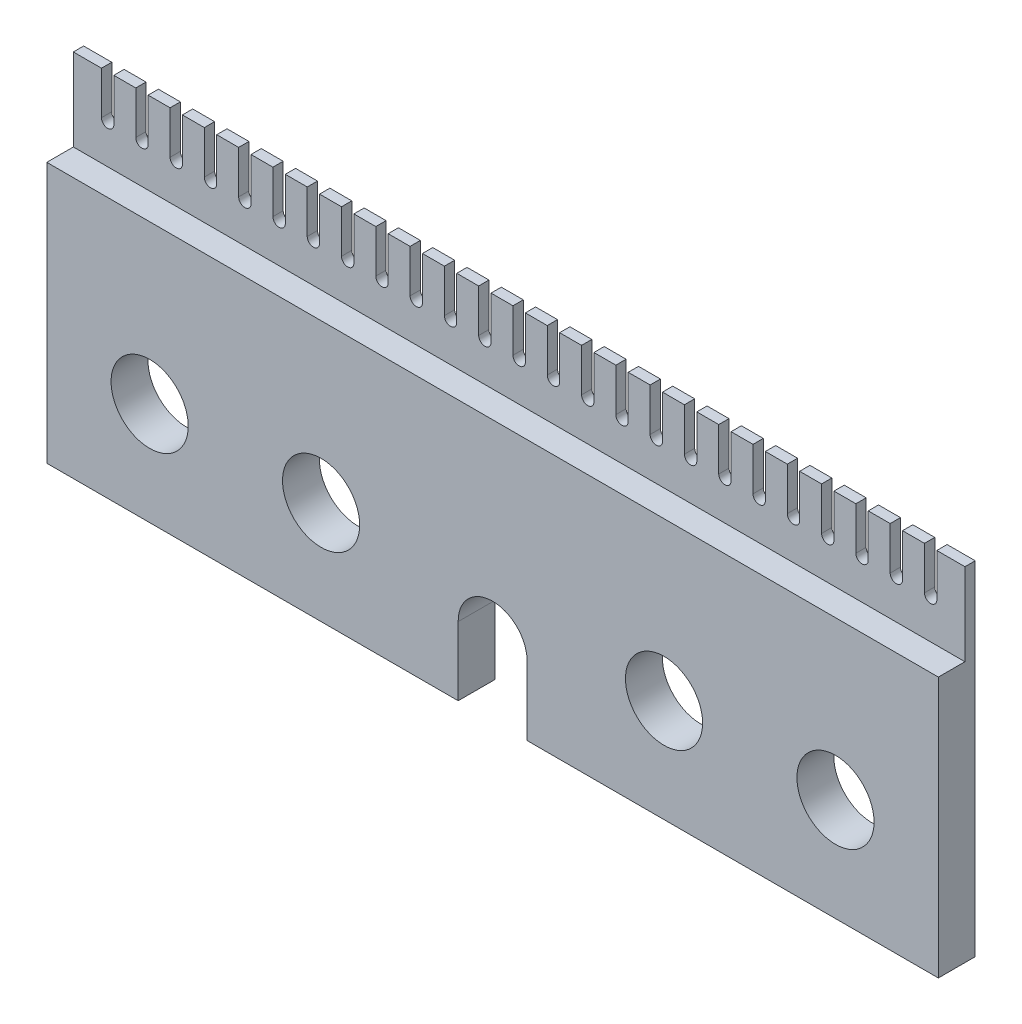
SolidWorks part; units mm, degrees
ref_plane "Front Plane" through (0, 0, 0) normal (0, 0, 1) x (1, 0, 0)
ref_plane "Top Plane" through (0, 0, 0) normal (0, 1, 0) x (1, 0, 0)
ref_plane "Right Plane" through (0, 0, 0) normal (1, 0, 0) x (0, 0, -1)
sketch "Sketch1" plane through (0, 0, 0) normal (0, 0, 1) x (1, 0, 0)
  line L0 (2.3988, -11.3273) -> (26.3844, -11.3273)
  line L1 (-25.6156, 8.6727) -> (-23.9756, 8.6727)
  line L2 (-25.6156, 8.6727) -> (-25.6156, -11.3273)
  line L3 (-25.6156, -11.3273) -> (-1.6212, -11.3273)
  line L4 (26.3844, 8.6727) -> (26.3844, -11.3273)
  line L5 (-23.2556, 8.6727) -> (-21.9756, 8.6727)
  line L6 (-1.6212, -11.3273) -> (-1.6212, -7.3273)
  line L7 (-21.2556, 8.6727) -> (-19.9756, 8.6727)
  line L8 (2.3988, -11.3273) -> (2.3988, -7.2968)
  line L9 (-21.2556, 8.6727) -> (-21.2556, 6.1727)
  line L10 (-23.9756, 8.6727) -> (-23.9756, 6.1727)
  line L11 (-21.9756, 8.6727) -> (-21.9756, 6.1727)
  line L12 (-23.2556, 8.6727) -> (-23.2556, 6.1727)
  line L13 (-19.2556, 8.6727) -> (-17.9756, 8.6727)
  line L14 (-19.2556, 8.6727) -> (-19.2556, 6.1727)
  line L15 (-19.9756, 8.6727) -> (-19.9756, 6.1727)
  line L16 (-17.2556, 8.6727) -> (-15.9756, 8.6727)
  line L17 (-17.2556, 8.6727) -> (-17.2556, 6.1727)
  line L18 (-17.9756, 8.6727) -> (-17.9756, 6.1727)
  line L19 (-15.2556, 8.6727) -> (-13.9756, 8.6727)
  line L20 (-15.2556, 8.6727) -> (-15.2556, 6.1727)
  line L21 (-15.9756, 8.6727) -> (-15.9756, 6.1727)
  line L22 (-13.2556, 8.6727) -> (-11.9756, 8.6727)
  line L23 (-13.2556, 8.6727) -> (-13.2556, 6.1727)
  line L24 (-13.9756, 8.6727) -> (-13.9756, 6.1727)
  line L25 (-11.2556, 8.6727) -> (-9.9756, 8.6727)
  line L26 (-11.2556, 8.6727) -> (-11.2556, 6.1727)
  line L27 (-11.9756, 8.6727) -> (-11.9756, 6.1727)
  line L28 (-9.2556, 8.6727) -> (-7.9756, 8.6727)
  line L29 (-9.2556, 8.6727) -> (-9.2556, 6.1727)
  line L30 (-9.9756, 8.6727) -> (-9.9756, 6.1727)
  line L31 (-7.2556, 8.6727) -> (-5.9756, 8.6727)
  line L32 (-7.2556, 8.6727) -> (-7.2556, 6.1727)
  line L33 (-7.9756, 8.6727) -> (-7.9756, 6.1727)
  line L34 (-5.2556, 8.6727) -> (-3.9756, 8.6727)
  line L35 (-5.2556, 8.6727) -> (-5.2556, 6.1727)
  line L36 (-5.9756, 8.6727) -> (-5.9756, 6.1727)
  line L37 (-3.2556, 8.6727) -> (-1.9756, 8.6727)
  line L38 (-3.2556, 8.6727) -> (-3.2556, 6.1727)
  line L39 (-3.9756, 8.6727) -> (-3.9756, 6.1727)
  line L40 (-1.2556, 8.6727) -> (0.0244, 8.6727)
  line L41 (-1.2556, 8.6727) -> (-1.2556, 6.1727)
  line L42 (-1.9756, 8.6727) -> (-1.9756, 6.1727)
  line L43 (0.7444, 8.6727) -> (2.0244, 8.6727)
  line L44 (0.7444, 8.6727) -> (0.7444, 6.1727)
  line L45 (0.0244, 8.6727) -> (0.0244, 6.1727)
  line L46 (2.7444, 8.6727) -> (4.0244, 8.6727)
  line L47 (2.7444, 8.6727) -> (2.7444, 6.1727)
  line L48 (2.0244, 8.6727) -> (2.0244, 6.1727)
  line L49 (4.7444, 8.6727) -> (6.0244, 8.6727)
  line L50 (4.7444, 8.6727) -> (4.7444, 6.1727)
  line L51 (4.0244, 8.6727) -> (4.0244, 6.1727)
  line L52 (6.7444, 8.6727) -> (8.0244, 8.6727)
  line L53 (6.7444, 8.6727) -> (6.7444, 6.1727)
  line L54 (6.0244, 8.6727) -> (6.0244, 6.1727)
  line L55 (8.7444, 8.6727) -> (10.0244, 8.6727)
  line L56 (8.7444, 8.6727) -> (8.7444, 6.1727)
  line L57 (8.0244, 8.6727) -> (8.0244, 6.1727)
  line L58 (10.7444, 8.6727) -> (12.0244, 8.6727)
  line L59 (10.7444, 8.6727) -> (10.7444, 6.1727)
  line L60 (10.0244, 8.6727) -> (10.0244, 6.1727)
  line L61 (12.7444, 8.6727) -> (14.0244, 8.6727)
  line L62 (12.7444, 8.6727) -> (12.7444, 6.1727)
  line L63 (12.0244, 8.6727) -> (12.0244, 6.1727)
  line L64 (14.7444, 8.6727) -> (16.0244, 8.6727)
  line L65 (14.7444, 8.6727) -> (14.7444, 6.1727)
  line L66 (14.0244, 8.6727) -> (14.0244, 6.1727)
  line L67 (16.7444, 8.6727) -> (18.0244, 8.6727)
  line L68 (16.7444, 8.6727) -> (16.7444, 6.1727)
  line L69 (16.0244, 8.6727) -> (16.0244, 6.1727)
  line L70 (18.7444, 8.6727) -> (20.0244, 8.6727)
  line L71 (18.7444, 8.6727) -> (18.7444, 6.1727)
  line L72 (18.0244, 8.6727) -> (18.0244, 6.1727)
  line L73 (20.7444, 8.6727) -> (22.0244, 8.6727)
  line L74 (20.7444, 8.6727) -> (20.7444, 6.1727)
  line L75 (20.0244, 8.6727) -> (20.0244, 6.1727)
  line L76 (22.7444, 8.6727) -> (24.0244, 8.6727)
  line L77 (22.7444, 8.6727) -> (22.7444, 6.1727)
  line L78 (22.0244, 8.6727) -> (22.0244, 6.1727)
  line L79 (24.7444, 8.6727) -> (26.0244, 8.6727)
  line L80 (24.7444, 8.6727) -> (24.7444, 6.1727)
  line L81 (24.0244, 8.6727) -> (24.0244, 6.1727)
  line L82 (26.0244, 8.6727) -> (26.3844, 8.6727)
  arc A0 (-23.9756, 6.1727) -> (-23.2556, 6.1727) centre (-23.6156, 6.1727) ccw
  arc A1 (2.3988, -7.2968) -> (-1.6212, -7.3273) centre (0.3887, -7.3038) ccw
  circle A2 centre (-19.6156, -5.3273) radius 2.25
  circle A3 centre (-9.6156, -5.3273) radius 2.25
  circle A4 centre (10.3844, -5.3273) radius 2.25
  circle A5 centre (20.3844, -5.3273) radius 2.25
  arc A6 (-21.9756, 6.1727) -> (-21.2556, 6.1727) centre (-21.6156, 6.1727) ccw
  arc A7 (-19.9756, 6.1727) -> (-19.2556, 6.1727) centre (-19.6156, 6.1727) ccw
  arc A8 (-17.9756, 6.1727) -> (-17.2556, 6.1727) centre (-17.6156, 6.1727) ccw
  arc A9 (-15.9756, 6.1727) -> (-15.2556, 6.1727) centre (-15.6156, 6.1727) ccw
  arc A10 (-13.9756, 6.1727) -> (-13.2556, 6.1727) centre (-13.6156, 6.1727) ccw
  arc A11 (-11.9756, 6.1727) -> (-11.2556, 6.1727) centre (-11.6156, 6.1727) ccw
  arc A12 (-9.9756, 6.1727) -> (-9.2556, 6.1727) centre (-9.6156, 6.1727) ccw
  arc A13 (-7.9756, 6.1727) -> (-7.2556, 6.1727) centre (-7.6156, 6.1727) ccw
  arc A14 (-5.9756, 6.1727) -> (-5.2556, 6.1727) centre (-5.6156, 6.1727) ccw
  arc A15 (-3.9756, 6.1727) -> (-3.2556, 6.1727) centre (-3.6156, 6.1727) ccw
  arc A16 (-1.9756, 6.1727) -> (-1.2556, 6.1727) centre (-1.6156, 6.1727) ccw
  arc A17 (0.0244, 6.1727) -> (0.7444, 6.1727) centre (0.3844, 6.1727) ccw
  arc A18 (2.0244, 6.1727) -> (2.7444, 6.1727) centre (2.3844, 6.1727) ccw
  arc A19 (4.0244, 6.1727) -> (4.7444, 6.1727) centre (4.3844, 6.1727) ccw
  arc A20 (6.0244, 6.1727) -> (6.7444, 6.1727) centre (6.3844, 6.1727) ccw
  arc A21 (8.0244, 6.1727) -> (8.7444, 6.1727) centre (8.3844, 6.1727) ccw
  arc A22 (10.0244, 6.1727) -> (10.7444, 6.1727) centre (10.3844, 6.1727) ccw
  arc A23 (12.0244, 6.1727) -> (12.7444, 6.1727) centre (12.3844, 6.1727) ccw
  arc A24 (14.0244, 6.1727) -> (14.7444, 6.1727) centre (14.3844, 6.1727) ccw
  arc A25 (16.0244, 6.1727) -> (16.7444, 6.1727) centre (16.3844, 6.1727) ccw
  arc A26 (18.0244, 6.1727) -> (18.7444, 6.1727) centre (18.3844, 6.1727) ccw
  arc A27 (20.0244, 6.1727) -> (20.7444, 6.1727) centre (20.3844, 6.1727) ccw
  arc A28 (22.0244, 6.1727) -> (22.7444, 6.1727) centre (22.3844, 6.1727) ccw
  arc A29 (24.0244, 6.1727) -> (24.7444, 6.1727) centre (24.3844, 6.1727) ccw
  dimension "D3" = 4.5
  dimension "D1" = 52
  dimension "D2" = 20
  dimension "D4" = 6
  dimension "D5" = 6
  dimension "D6" = 16
  dimension "D7" = 36
  dimension "D8" = 46
  dimension "D10" = 4
  dimension "D11" = 4.02
  dimension "D12" = 2
  dimension "D13" = 0.36
  dimension "D14" = 17.5
  dimension "D15" = 1.28
  dimension "D17" = 20
  dimension "D16" = 25
extrude "Boss-Extrude1" add sketch "Sketch1" along normal blind 2.15
sketch "Sketch2" plane through (-25.6156, 0, 0) normal (-1, 0, 0) x (0, 0, 1)
  line L1 (2.15, 8.6727) -> (0.6, 8.6727)
  line L2 (2.15, 8.6727) -> (2.15, 3.8727)
  line L3 (2.15, 3.8727) -> (0.6, 3.8727)
  line L4 (0.6, 8.6727) -> (0.6, 3.8727)
  dimension "D1" = 1.55
  dimension "D2" = 4.8
extrude "Cut-Extrude1" cut sketch "Sketch2" against normal through all
